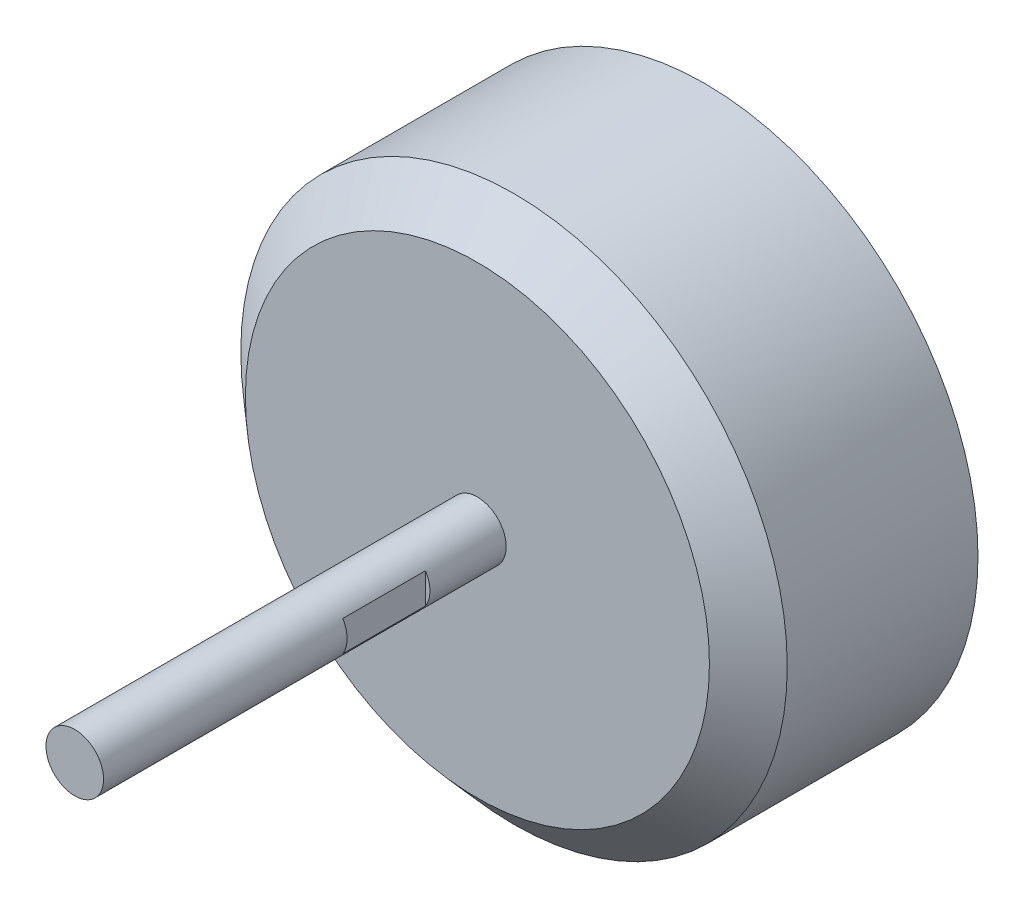
SolidWorks part; units mm, degrees
ref_plane "Front Plane" through (0, 0, 0) normal (0, 0, 1) x (1, 0, 0)
ref_plane "Top Plane" through (0, 0, 0) normal (0, 1, 0) x (1, 0, 0)
ref_plane "Right Plane" through (0, 0, 0) normal (1, 0, 0) x (0, 0, -1)
sketch "Sketch1" plane through (0, 0, 0) normal (0, 0, 1) x (1, 0, 0)
  circle A0 centre (0, 0) radius 14.325
  circle A1 centre (0, 0) radius 13.825
  dimension "D1" = 28.65
  dimension "D2" = 27.65
extrude "Boss-Extrude1" add sketch "Sketch1" along normal blind 10
sketch "Sketch2" plane through (0, 0, 10) normal (0, 0, 1) x (1, 0, 0)
  circle A0 centre (0, 0) radius 14.325
  dimension "D1" = 28.65
ref_plane "Plane4" through (0, 0, 11.92) normal (0, 0, 1) x (1, 0, 0)
sketch "Sketch3" plane through (0, 0, 11.92) normal (0, 0, 1) x (1, 0, 0)
  circle A0 centre (0, 0) radius 12.165
  dimension "D1" = 24.33
loft "Loft1" add profiles "Sketch2", "Sketch3"
sketch "Sketch5" plane through (0, 0, 11.92) normal (0, 0, 1) x (1, 0, 0)
  circle A0 centre (0, 0) radius 1.51
  dimension "D1" = 3.02
extrude "Boss-Extrude3" add sketch "Sketch5" along normal blind 21.11 and the other way blind 17.23
sketch "Sketch6" plane through (0, 0, 0) normal (0, 1, 0) x (1, 0, 0)
  line L0 (-55, -11.92) -> (55, -11.92) construction
  line L1 (-1.28, -15.92) -> (-2.28, -15.92)
  line L2 (-1.28, -15.92) -> (-1.28, -20.26)
  line L3 (-1.28, -20.26) -> (-2.28, -20.26)
  line L4 (-2.28, -15.92) -> (-2.28, -20.26)
  line L6 (0, -15.7575) -> (0, 15.7575) construction
  line L7 (1.28, -20.26) -> (2.28, -20.26)
  line L8 (2.28, -15.92) -> (2.28, -20.26)
  line L9 (1.28, -15.92) -> (2.28, -15.92)
  line L10 (1.28, -15.92) -> (1.28, -20.26)
  dimension "D1" = 4
  dimension "D2" = 1
  dimension "D3" = 4.34
  dimension "D4" = 1.28
extrude "Cut-Extrude1" cut sketch "Sketch6" against normal through all both and the other way through all
